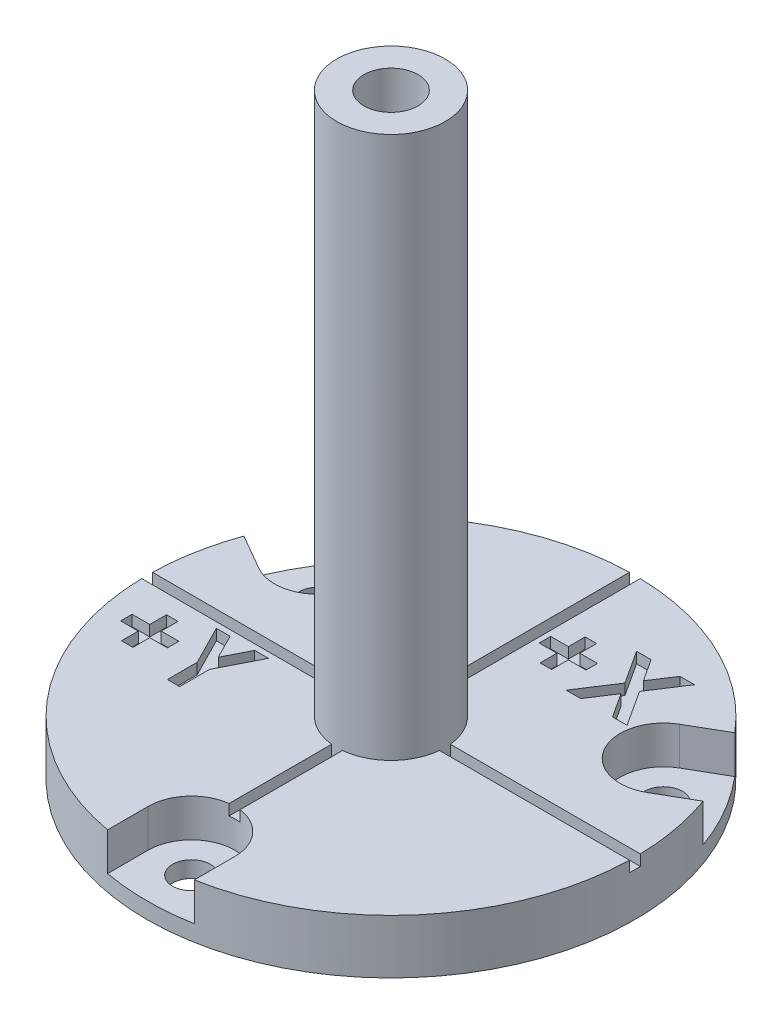
SolidWorks part; units mm, degrees
ref_plane "Front" through (0, 0, 0) normal (0, 0, 1) x (1, 0, 0)
ref_plane "Top" through (0, 0, 0) normal (0, 1, 0) x (1, 0, 0)
ref_plane "Right" through (0, 0, 0) normal (1, 0, 0) x (0, 0, -1)
sketch "Sketch1" plane through (0, 0, 0) normal (0, 1, 0) x (1, 0, 0)
  line L0 (0, 22.5) -> (0, -22.5) construction
  line L1 (22.5, 0) -> (-22.5, 0) construction
  circle A0 centre (0, 0) radius 22.5
  circle A1 centre (0, 0) radius 18.4 construction
  arc A2 (-10.9795, -19.6393) -> (-7.9114, -21.0632) centre (-9.4455, -20.3512) cw construction
  point P19 (0, 0)
  dimension "D1" = 45
  dimension "D2" = 36.8
extrude "plate" add sketch "Sketch1" along normal blind 5
sketch "Sketch6" plane through (0, 5, 0) normal (0, 1, 0) x (1, 0, 0)
  line L0 (0, 22.5) -> (0, -22.5) construction
  line L1 (0, -22.5) -> (0, -18.4) construction
  line L2 (-4, -22.5) -> (-4, -18.4)
  line L3 (4, -22.5) -> (4, -18.4)
  circle A1 centre (0, 0) radius 18.4 construction
  circle A2 centre (0, 0) radius 22.5 construction
  arc A3 (-4, -22.5) -> (4, -22.5) centre (0, -22.5) ccw
  arc A4 (4, -18.4) -> (-4, -18.4) centre (0, -18.4) ccw
  point P7 (0, -20.45)
  dimension "D1" = 4
extrude "opening for screw" cut sketch "Sketch6" against normal blind 5 from offset 1.5 contours L3 A4 L2 A3
sketch "Sketch7" plane through (0, 1.5, 0) normal (0, 1, 0) x (1, 0, 0)
  line L0 (0, 22.5) -> (0, -22.5) construction
  circle A0 centre (0, -18.4) radius 1.75
  circle A1 centre (0, 0) radius 18.4 construction
  dimension "D1" = 3.5
extrude "screw hole" cut sketch "Sketch7" against normal blind 5
pattern_circular "CirPattern20" count 3 over 360 about axis through (0, 0, 0) along (0, 1, 0) of "opening for screw", "screw hole"
sketch "Sketch10" plane through (0, 5, 0) normal (0, 1, 0) x (1, 0, 0)
  line L1 (-22.5, 0.5) -> (22.5, 0.5)
  line L2 (-22.5, 0.5) -> (-22.5, -0.5)
  line L3 (-22.5, -0.5) -> (22.5, -0.5)
  line L4 (22.5, 0.5) -> (22.5, -0.5)
  line L5 (-0.5, 22.5) -> (0.5, 22.5)
  line L6 (-0.5, 22.5) -> (-0.5, -22.5)
  line L7 (-0.5, -22.5) -> (0.5, -22.5)
  line L8 (0.5, 22.5) -> (0.5, -22.5)
  line L9 (0, 22.5) -> (0, -22.5) construction
  point P4 (22.5, 0)
  point P9 (-22.5, 0)
  point P14 (0, -22.5)
  point P15 (0, 22.5)
  dimension "D1" = 1
  dimension "D2" = 1
extrude "Cut-Extrude5" cut sketch "Sketch10" against normal blind 1 contours L6 L7 L8 L5 | L1 L4 L3 L2
sketch "Sketch11" plane through (0, 5, 0) normal (0, 1, 0) x (1, 0, 0)
  line L0 (0.5, 22.4944) -> (0.5, 0.5) construction
  text T0 "<b>+X</b>"
  text T1 "<b>+Y</b>"
extrude "Cut-Extrude6" cut sketch "Sketch11" against normal blind 1
sketch "Sketch12" plane through (0, 5, 0) normal (0, 1, 0) x (1, 0, 0)
  circle A0 centre (0, 0) radius 5
  circle A1 centre (0, 0) radius 2.5
  dimension "D1" = 5
  dimension "D2" = 10
extrude "Boss-Extrude2" add sketch "Sketch12" along normal blind 50 and the other way up to surface (1 mm away)
